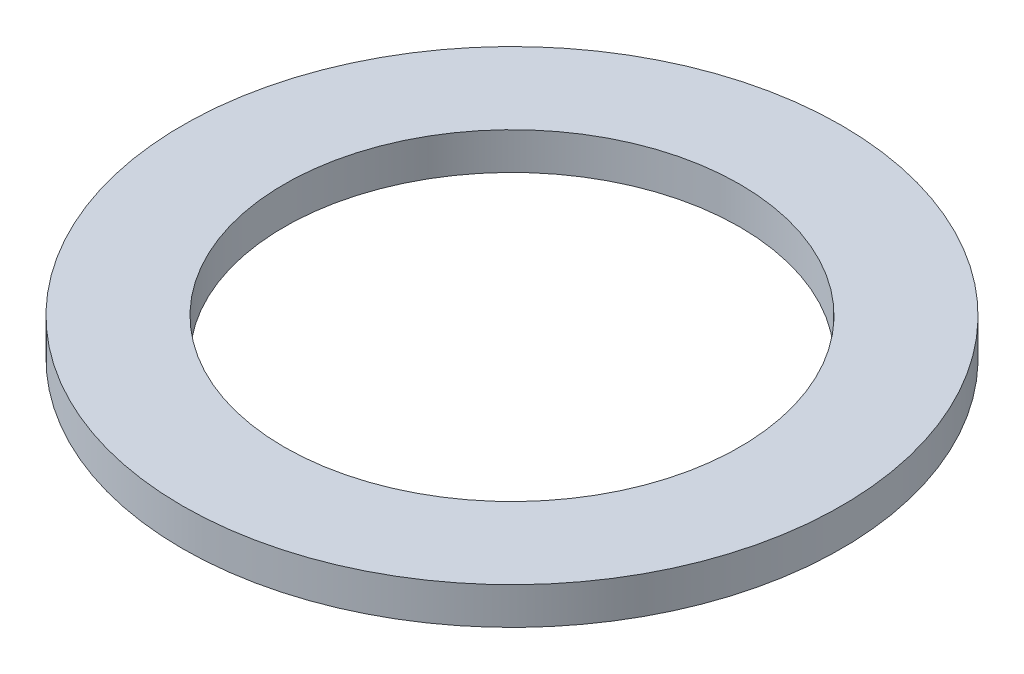
SolidWorks part; units mm, degrees
ref_plane "Front Plane" through (0, 0, 0) normal (0, 0, 1) x (1, 0, 0)
ref_plane "Top Plane" through (0, 0, 0) normal (0, 1, 0) x (1, 0, 0)
ref_plane "Right Plane" through (0, 0, 0) normal (1, 0, 0) x (0, 0, -1)
sketch "Sketch1" plane through (0, 0, 0) normal (0, 1, 0) x (1, 0, 0)
  circle A0 centre (0, 0) radius 2.2606
  dimension "OD" = 4.5212
extrude "Boss-Extrude1" add sketch "Sketch1" along normal blind 0.254
sketch "Sketch5" plane through (0, 0.254, 0) normal (0, 1, 0) x (-1, 0, 0)
  circle A0 centre (0, 0) radius 1.5621
  dimension "ID" = 3.1242
extrude "Cut-Extrude1" cut sketch "Sketch5" against normal through all
